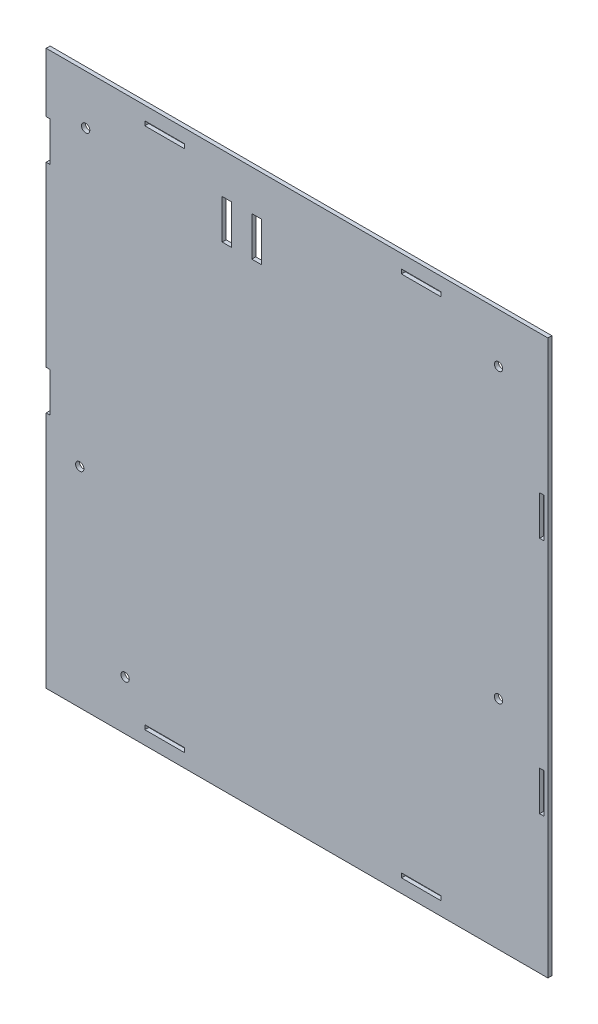
SolidWorks part; units mm, degrees
material "Acrylic (Medium-high impact)"
ref_plane "Front Plane" through (0, 0, 0) normal (0, 0, 1) x (1, 0, 0)
ref_plane "Top Plane" through (0, 0, 0) normal (0, 1, 0) x (1, 0, 0)
ref_plane "Right Plane" through (0, 0, 0) normal (1, 0, 0) x (0, 0, -1)
sketch "Sketch1" plane through (0, 0, 0) normal (0, 0, 1) x (1, 0, 0)
  line L0 (-70, 268.6) -> (-50, 268.6)
  line L1 (-250, -5.4333) -> (4.2, -5.4333)
  line L2 (-250, -5.4333) -> (-250, 275.4333)
  line L3 (-250, 275.4333) -> (4.2, 275.4333)
  line L4 (4.2, -5.4333) -> (4.2, 275.4333)
  line L5 (2, 275.4333) -> (0, 275.4333) construction
  line L6 (-70, 268.6) -> (-70, 266.4)
  line L7 (-70, 266.4) -> (-50, 266.4)
  line L8 (-250, 135) -> (4.2, 135) construction
  line L9 (-50, 268.6) -> (-50, 266.4)
  line L10 (-70, 267.5) -> (-50, 267.5) construction
  line L11 (-60, 268.6) -> (-60, 266.4) construction
  line L12 (-190, 1.4) -> (-190, 3.6) construction
  line L13 (2.2, 74.5667) -> (0, 74.5667) construction
  line L14 (1.1, 64.5667) -> (1.1, 84.5667) construction
  line L15 (2.2, 64.5667) -> (2.2, 84.5667)
  line L16 (0, 84.5667) -> (2.2, 84.5667)
  line L17 (0, 64.5667) -> (0, 84.5667)
  line L18 (0, 64.5667) -> (2.2, 64.5667)
  line L19 (-200, 2.5) -> (-180, 2.5) construction
  line L20 (-60, 1.4) -> (-60, 3.6) construction
  line L21 (-70, 2.5) -> (-50, 2.5) construction
  line L22 (-180, 1.4) -> (-180, 3.6)
  line L23 (-200, 3.6) -> (-180, 3.6)
  line L24 (-200, 1.4) -> (-200, 3.6)
  line L25 (0, 205.4333) -> (2, 205.4333) construction
  line L26 (0, 205.4333) -> (2.2, 205.4333)
  line L27 (0, 205.4333) -> (0, 185.4333)
  line L28 (0, 185.4333) -> (2.2, 185.4333)
  line L29 (2.2, 205.4333) -> (2.2, 185.4333)
  line L30 (0, 205.4333) -> (2, 205.4333) construction
  line L31 (-200, 1.4) -> (-180, 1.4)
  line L32 (-50, 1.4) -> (-50, 3.6)
  line L33 (-70, 3.6) -> (-50, 3.6)
  line L34 (-200, 268.6) -> (-180, 268.6)
  line L35 (-200, 268.6) -> (-200, 266.4)
  line L36 (-200, 266.4) -> (-180, 266.4)
  line L37 (-180, 268.6) -> (-180, 266.4)
  line L38 (-70, 1.4) -> (-70, 3.6)
  line L39 (-70, 1.4) -> (-50, 1.4)
  line L47 (2, -5.4333) -> (0, -5.4333) construction
  line L48 (-250, 2) -> (-250, 0) construction
  line L49 (-200, 267.5) -> (-180, 267.5) construction
  line L50 (-190, 268.6) -> (-190, 266.4) construction
  line L51 (1.1, 205.4333) -> (1.1, 185.4333) construction
  line L52 (2.2, 195.4333) -> (0, 195.4333) construction
  point P4 (1.1, 205.4333)
  point P5 (0, 195.4333)
  point P6 (-200, 267.5)
  point P9 (-250, 135)
  point P10 (-122.9, -5.4333)
  point P11 (4.2, 135)
  point P12 (-122.9, 275.4333)
  point P17 (-70, 267.5)
  point P22 (-50, 267.5)
  point P23 (-60, 268.6)
  point P24 (-60, 266.4)
  point P29 (-60, 267.5)
  point P43 (2.2, 195.4333)
  point P46 (1.1, 185.4333)
  point P55 (1.1, 195.4333)
  point P60 (1.1, 74.5667)
  point P61 (1.1, 84.5667)
  point P62 (2.2, 74.5667)
  point P63 (0, 74.5667)
  point P64 (1.1, 64.5667)
  point P71 (-180, 267.5)
  point P72 (-190, 268.6)
  point P73 (-190, 266.4)
  point P78 (-190, 267.5)
  point P88 (-190, 2.5)
  point P89 (-190, 3.6)
  point P90 (-190, 1.4)
  point P91 (-180, 2.5)
  point P92 (-60, 2.5)
  point P93 (-60, 3.6)
  point P94 (-60, 1.4)
  point P95 (-50, 2.5)
  point P96 (-70, 2.5)
  point P97 (-200, 2.5)
  dimension "D2" = 50
  dimension "D3" = 250
  dimension "D4" = 2
  dimension "D5" = 110
  dimension "D6" = 2
  dimension "D10" = 2.2
  dimension "D11" = 20
  dimension "D14" = 7.9333
  dimension "D17" = 20
extrude "Boss-Extrude1" add sketch "Sketch1" along normal blind 2
sketch "Sketch2" plane through (0, 0, 2) normal (0, 0, 1) x (1, 0, 0)
  line L0 (-145.9052, 255) -> (-140.9052, 255) construction
  line L1 (-145.8052, 255) -> (-141.0052, 255)
  line L2 (-145.8052, 255) -> (-145.8052, 235)
  line L3 (-145.8052, 235) -> (-141.0052, 235)
  line L4 (-141.0052, 255) -> (-141.0052, 235)
  line L5 (-145.9052, 235) -> (-140.9052, 235) construction
  line L6 (-145.9052, 235) -> (-145.9052, 255) construction
  line L8 (-156.0052, 235) -> (-160.8052, 235)
  line L9 (-156.0052, 235) -> (-156.0052, 255)
  line L10 (-156.0052, 255) -> (-160.8052, 255)
  line L11 (-160.8052, 235) -> (-160.8052, 255)
  dimension "D1" = 4.8
  dimension "D2" = 0.1
  dimension "D3" = 4.8
  dimension "D4" = 15
extrude "Cut-Extrude1" cut sketch "Sketch2" against normal blind 5
sketch "Sketch3" plane through (0, 0, 2) normal (0, 0, 1) x (1, 0, 0)
  line L0 (4.2, 275.4333) -> (-250, 275.4333) construction
  line L1 (-250, 275.4333) -> (-250, -5.4333) construction
  line L2 (4.2, -5.4333) -> (4.2, 275.4333) construction
  circle A0 centre (-230, 250.4333) radius 2.1
  circle A1 centre (-20.8, 250.4333) radius 2.1
  dimension "D1" = 4.2
  dimension "D2" = 4.2
  dimension "D3" = 25
  dimension "D4" = 20
  dimension "D5" = 25
  dimension "D6" = 25
extrude "Cut-Extrude2" cut sketch "Sketch3" against normal blind 5
sketch "Sketch4" plane through (0, 0, 2) normal (0, 0, 1) x (1, 0, 0)
  line L0 (-250, -5.4333) -> (4.2, -5.4333) construction
  line L1 (-250, 275.4333) -> (-250, -5.4333) construction
  circle A0 centre (-210, 19.5667) radius 2.1
  dimension "D1" = 25
  dimension "D2" = 40
  dimension "D3" = 4.2
extrude "Cut-Extrude3" cut sketch "Sketch4" against normal blind 5
sketch "Sketch5" plane through (0, 0, 2) normal (0, 0, 1) x (1, 0, 0)
  line L0 (4.2, -5.4333) -> (4.2, 275.4333) construction
  line L1 (-250, -5.4333) -> (4.2, -5.4333) construction
  circle A0 centre (-20.8, 104.5667) radius 2.1
  dimension "D1" = 4.2
  dimension "D2" = 25
  dimension "D3" = 110
extrude "Cut-Extrude4" cut sketch "Sketch5" against normal blind 5
sketch "Sketch6" plane through (0, 0, 2) normal (0, 0, 1) x (1, 0, 0)
  circle A0 centre (-233, 100.4333) radius 2.1
  dimension "D1" = 4.2
extrude "Cut-Extrude5" cut sketch "Sketch6" against normal blind 5
sketch "Sketch7" plane through (0, 0, 2) normal (0, 0, 1) x (1, 0, 0)
  line L1 (-250, 245.4333) -> (-248, 245.4333)
  line L2 (-250, 245.4333) -> (-250, 225.4333)
  line L3 (-250, 225.4333) -> (-248, 225.4333)
  line L4 (-248, 245.4333) -> (-248, 225.4333)
  line L5 (-250, 135.4333) -> (-248, 135.4333)
  line L6 (-250, 135.4333) -> (-250, 115.4333)
  line L7 (-250, 115.4333) -> (-248, 115.4333)
  line L8 (-248, 135.4333) -> (-248, 115.4333)
  dimension "D1" = 20
  dimension "D2" = 2
  dimension "D4" = 20
extrude "Cut-Extrude6" cut sketch "Sketch7" against normal blind 10
